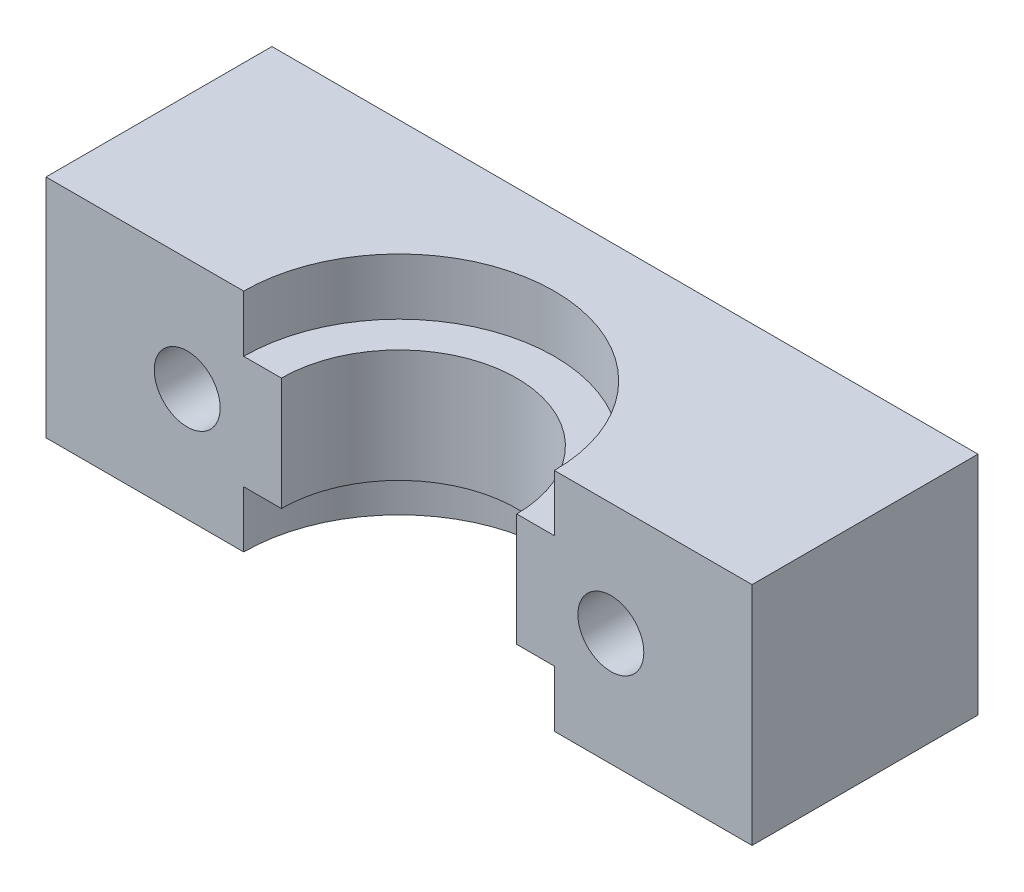
SolidWorks part; units mm, degrees
ref_plane "Front Plane" through (0, 0, 0) normal (0, 0, 1) x (1, 0, 0)
ref_plane "Top Plane" through (0, 0, 0) normal (0, 1, 0) x (1, 0, 0)
ref_plane "Right Plane" through (0, 0, 0) normal (1, 0, 0) x (0, 0, -1)
sketch "Sketch1" plane through (0, 0, 0) normal (0, 1, 0) x (1, 0, 0)
  line L0 (-6.25, 0) -> (-18.75, 0)
  line L5 (-18.75, 0) -> (-18.75, 12)
  line L6 (0, 0) -> (0, 6.25) construction
  line L7 (6.25, 0) -> (18.75, 0)
  line L8 (18.75, 0) -> (18.75, 12)
  line L9 (-18.75, 12) -> (18.75, 12)
  arc A0 (6.25, 0) -> (-6.25, 0) centre (0, 0) ccw
  dimension "D1" = 12.5
  dimension "D2" = 12.5
  dimension "D3" = 12
extrude "Boss-Extrude1" add sketch "Sketch1" along normal mid plane 12
sketch "Sketch2" plane through (0, 0, 0) normal (0, 1, 0) x (1, 0, 0)
  circle A0 centre (0, 0) radius 8.25
  dimension "D1" = 16.5
extrude "Cut-Extrude1" cut sketch "Sketch2" along normal up to next from offset 3
mirror "Mirror1" about plane through (0, 0, 0) normal (0, 1, 0) of "Cut-Extrude1"
sketch "Sketch3" plane through (0, 0, 0) normal (0, 0, 1) x (1, 0, 0)
  line L0 (0, 6) -> (0, -6) construction
  line L1 (8.25, 6) -> (-8.25, 6) construction
  line L2 (-8.25, -6) -> (8.25, -6) construction
  line L3 (-18.75, 0) -> (-6.25, 0) construction
  line L4 (-18.75, 6) -> (-18.75, -6) construction
  line L5 (-6.25, 3) -> (-6.25, -3) construction
  circle A0 centre (-11.25, 0) radius 1.75
  circle A1 centre (11.25, 0) radius 1.75
  point P16 (-11.8092, 0)
  dimension "D1" = 3.5
  dimension "D2" = 11.25
extrude "Cut-Extrude2" cut sketch "Sketch3" against normal up to next
sketch "Sketch4" plane through (0, 0, -12) normal (0, 0, -1) x (-1, 0, 0)
  line L0 (0, -6) -> (0, 6) construction
  line L1 (-18.75, -6) -> (18.75, -6) construction
  line L2 (-18.75, 6) -> (18.75, 6) construction
  circle A0 centre (11.25, 0) radius 3
  circle A1 centre (-11.25, 0) radius 3
  dimension "D1" = 6
extrude "Cut-Extrude3" cut sketch "Sketch4" against normal blind 3 and the other way through all
